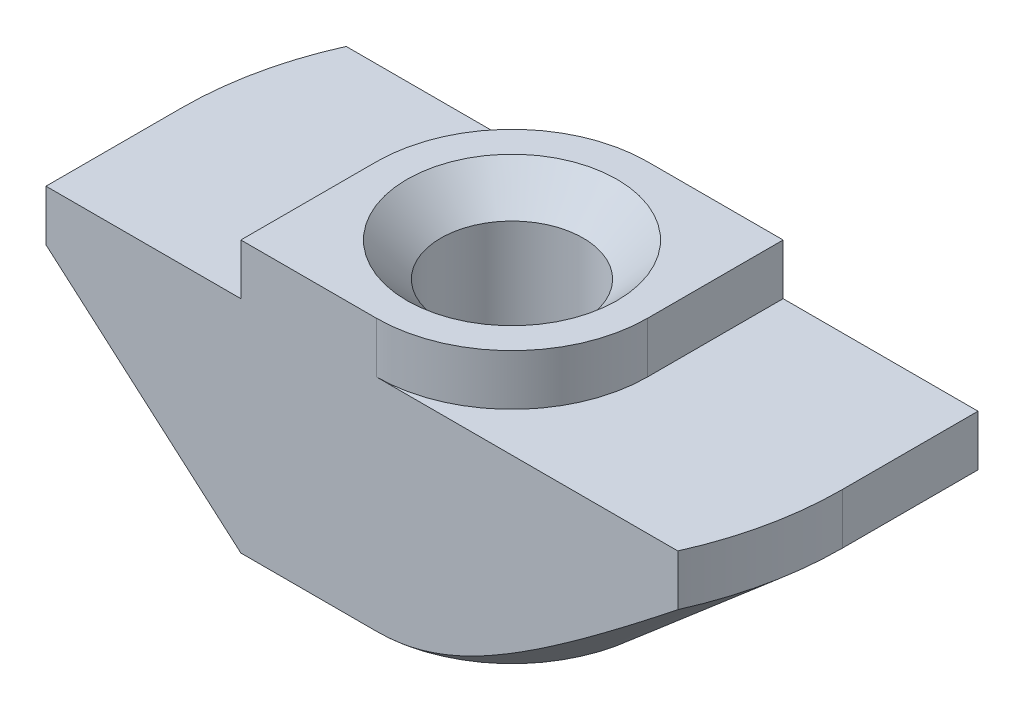
SolidWorks part; units mm, degrees
material "Сталь 20  ГОСТ 1050-2013"
ref_plane "Спереди" through (0, 0, 0) normal (0, 0, 1) x (1, 0, 0)
ref_plane "Сверху" through (0, 0, 0) normal (0, 1, 0) x (1, 0, 0)
ref_plane "Справа" through (0, 0, 0) normal (1, 0, 0) x (0, 0, -1)
sketch "Эскиз1" plane through (0, 0, 0) normal (0, 0, 1) x (1, 0, 0)
  line L0 (4, 0) -> (-4, 0)
  line L1 (-4, 0) -> (-4, -1.5)
  line L2 (-4, -1.5) -> (-9.75, -1.5)
  line L3 (-9.75, -1.5) -> (-9.75, -8)
  line L4 (-9.75, -8) -> (9.75, -8)
  line L5 (0, -8) -> (0, 0) construction
  line L6 (9.75, -1.5) -> (9.75, -8)
  line L7 (4, -1.5) -> (9.75, -1.5)
  line L8 (4, 0) -> (4, -1.5)
  dimension "D1" = 8
  dimension "D2" = 19.5
  dimension "D3" = 8
  dimension "D4" = 1.5
extrude "Бобышка-Вытянуть1" add sketch "Эскиз1" along normal mid plane 8
hole_wizard "Отверстие обработанное метчиком M53" positions "Эскиз2" profile "Эскиз3" tap size "M5" standard "ISO" end condition up to next
sketch "Эскиз2" plane through (0, 0, 0) normal (0, 1, 0) x (1, 0, 0)
  point P0 (0, 0)
sketch "Эскиз3" plane through (0, 0, 0) normal (1, 0, 0) x (0, 0, 1)
  line L0 (0, 0) -> (0, 8)
  line L1 (0, 8) -> (3.1, 8)
  line L2 (2.1, 7) -> (2.1, 1)
  line L3 (2.1, 1) -> (3.1, 0)
  line L5 (3.1, 0) -> (0, 0)
  line L6 (-2.1, 1) -> (-3.1, 0) construction
  line L7 (3.1, 8) -> (2.1, 7)
  line L8 (-3.1, 8) -> (-2.1, 7) construction
  line L11 (0, -6.35) -> (0, 107.95) construction
  dimension "Диаметр проходного сверла" = 4.2
  dimension "Глубина проходного сверла" = 8
  dimension "Диаметр передней зенковки" = 6.2
  dimension "Угол передней зенковки" = 90
  dimension "Диаметр задней зенковки" = 6.2
  dimension "Угол задней зенковки" = 90
cosmetic thread "Отверстие резьбы1" parameters "D2"=5
sketch "Эскиз4" plane through (0, 0, 0) normal (0, 1, 0) x (1, 0, 0)
  line L0 (-4, 4) -> (-4, 0)
  line L1 (-4, -4) -> (-4, 4) construction
  line L2 (4, 4) -> (-4, 4) construction
  line L3 (0, 4) -> (-4, 4)
  line L4 (0, -4) -> (4, -4)
  line L5 (4, -4) -> (-4, -4) construction
  line L6 (4, -4) -> (4, 0)
  line L7 (4, -4) -> (4, 4) construction
  arc A0 (-4, 0) -> (0, 4) centre (0, 0) cw
  arc A1 (4, 0) -> (0, -4) centre (0, 0) cw
extrude "Вырез-Вытянуть1" cut sketch "Эскиз4" against normal up to surface (1.5 mm away) up to face at (-6.875, -1.5, 0)
sketch "Эскиз5" plane through (0, -1.5, 0) normal (0, 1, 0) x (1, 0, 0)
  line L0 (-9.75, 0) -> (-9.75, 4)
  line L1 (-9.75, -4) -> (-9.75, 4) construction
  line L2 (-9.75, 4) -> (-8.8917, 4)
  line L3 (0, 4) -> (-9.75, 4) construction
  line L4 (9.75, 0) -> (9.75, -4)
  line L5 (9.75, -4) -> (9.75, 4) construction
  line L6 (9.75, -4) -> (8.8917, -4)
  line L7 (9.75, -4) -> (0, -4) construction
  arc A0 (-8.8917, 4) -> (-9.75, 0) centre (0, 0) ccw
  arc A2 (9.75, 0) -> (8.8917, -4) centre (0, 0) cw
  point P19 (0, 0)
extrude "Вырез-Вытянуть2" cut sketch "Эскиз5" against normal through all
sketch "Эскиз6" plane through (0, 0, 4) normal (0, 0, 1) x (1, 0, 0)
  line L0 (-9.75, -3) -> (-9.75, -8)
  line L1 (-9.75, -1.5) -> (-9.75, -8) construction
  line L2 (-9.75, -8) -> (-4, -8)
  line L3 (-9.75, -8) -> (8.8917, -8) construction
  line L4 (-4, -8) -> (-9.75, -3)
  line L5 (-4, -1.5) -> (-9.75, -1.5) construction
  line L6 (-4, 0) -> (-4, -1.5) construction
  point P10 (0, 0)
  dimension "D1" = 1.5
sketch "Эскиз7" plane through (0, -8, 0) normal (0, -1, 0) x (1, 0, 0)
  line L0 (0, 9.75) -> (-9.75, 9.75)
  line L1 (-9.75, 9.75) -> (-9.75, 0)
  line L2 (0, -9.75) -> (9.75, -9.75)
  line L3 (9.75, -9.75) -> (9.75, 0)
  arc A0 (-9.75, 0) -> (0, -9.75) centre (0, 0) ccw
  arc A1 (9.75, 0) -> (0, 9.75) centre (0, 0) ccw
sweep "Вырез-По траектории1" cut profiles "Эскиз6" path "Эскиз7"
